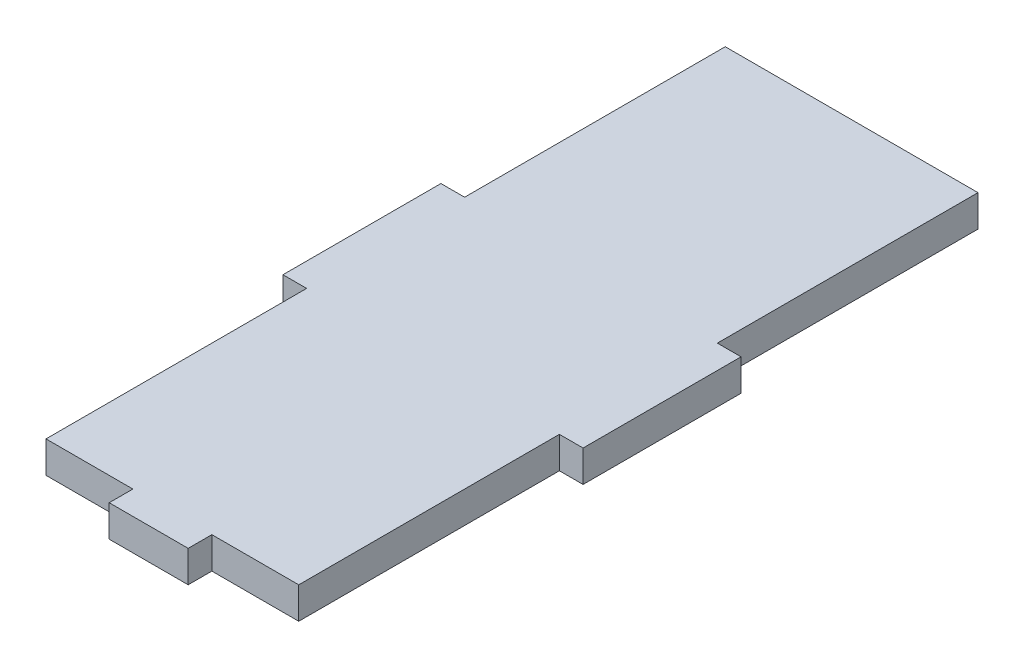
SolidWorks part; units mm, degrees
material "Acier S235"
ref_plane "Plan de face" through (0, 0, 0) normal (0, 0, 1) x (1, 0, 0)
ref_plane "Plan de dessus" through (0, 0, 0) normal (0, 1, 0) x (1, 0, 0)
ref_plane "Plan de droite" through (0, 0, 0) normal (1, 0, 0) x (0, 0, -1)
sketch "Esquisse1" plane through (0, 0, 0) normal (0, 1, 0) x (1, 0, 0)
  line L0 (-16, -10) -> (-16, -43)
  line L1 (-19, -46) -> (19, -46) construction
  line L2 (-19, -46) -> (-19, 43) construction
  line L3 (-19, 43) -> (19, 43) construction
  line L4 (19, -46) -> (19, 43) construction
  line L5 (-16, -10) -> (-19, -10)
  line L6 (-19, -10) -> (-19, 10)
  line L7 (-19, 10) -> (-16, 10)
  line L8 (-16, 10) -> (-16, 43)
  line L13 (-16, 43) -> (16, 43)
  line L14 (16, 43) -> (16, 10)
  line L15 (16, 10) -> (19, 10)
  line L16 (19, 10) -> (19, -10)
  line L17 (19, -10) -> (16, -10)
  line L18 (16, -10) -> (16, -43)
  line L19 (16, -43) -> (5, -43)
  line L20 (5, -43) -> (5, -46)
  line L21 (5, -46) -> (-5, -46)
  line L22 (-5, -46) -> (-5, -43)
  line L23 (-5, -43) -> (-16, -43)
  point P0 (0, 0)
  point P6 (0, 0)
  point P8 (0, 0)
  point P14 (15.1128, -40.8723)
  point P28 (-19, 0)
  point P29 (0, -46)
  dimension "D1" = 38
  dimension "D2" = 89
  dimension "D3" = 20
  dimension "D4" = 33
  dimension "D5" = 10
  dimension "D6" = 11
extrude "Boss.-Extru.1" add sketch "Esquisse1" along normal blind 4
